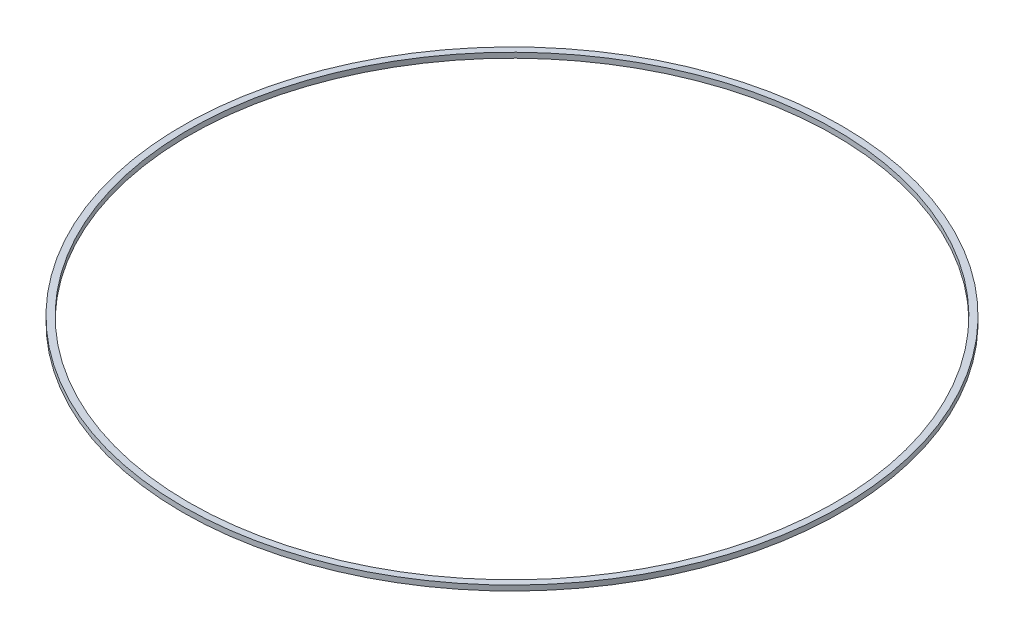
SolidWorks part; units mm, degrees
ref_plane "Front Plane" through (0, 0, 0) normal (0, 0, 1) x (1, 0, 0)
ref_plane "Top Plane" through (0, 0, 0) normal (0, 1, 0) x (1, 0, 0)
ref_plane "Right Plane" through (0, 0, 0) normal (1, 0, 0) x (0, 0, -1)
sketch "Sketch1" plane through (0, 0, 0) normal (0, 1, 0) x (1, 0, 0)
  circle A0 centre (0, 0) radius 24.9
  circle A1 centre (0, 0) radius 25.4
  dimension "D1" = 50.8
  dimension "D2" = 0.5
extrude "Boss-Extrude1" add sketch "Sketch1" along normal blind 0.4
